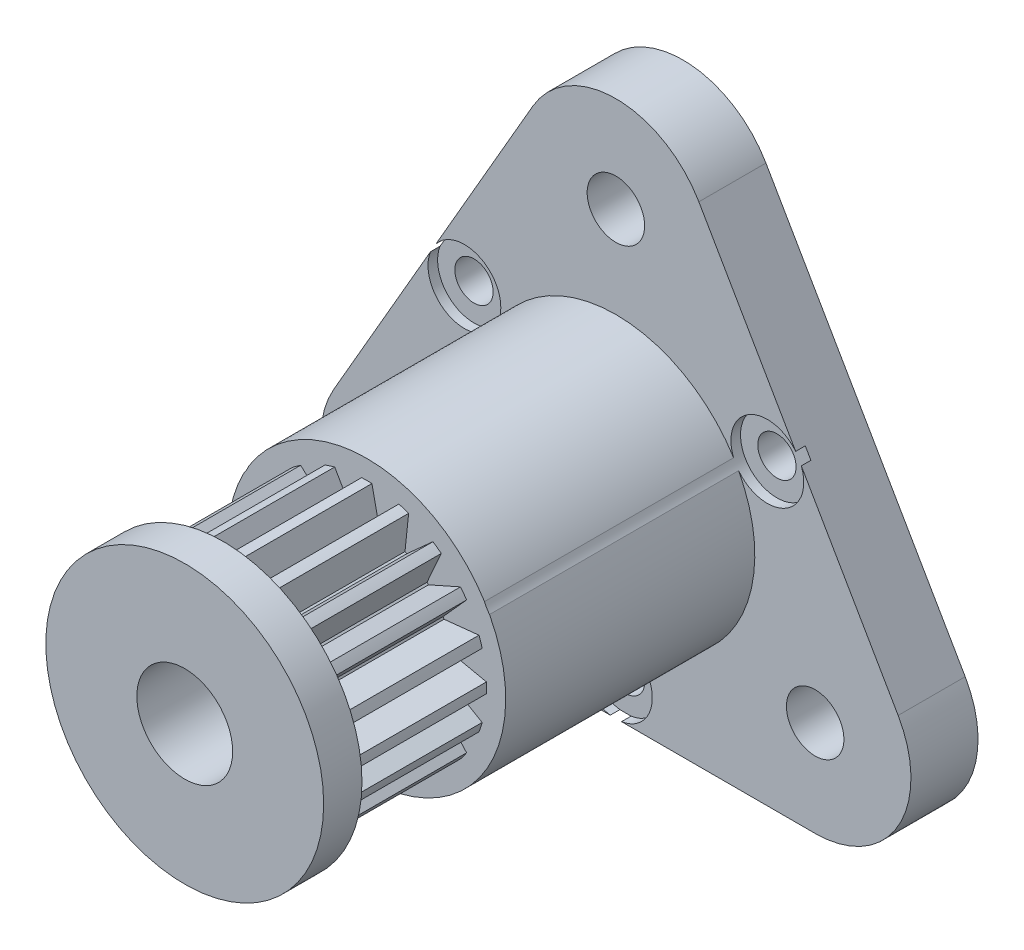
SolidWorks part; units mm, degrees
ref_plane "Front Plane" through (0, 0, 0) normal (0, 0, 1) x (1, 0, 0)
ref_plane "Top Plane" through (0, 0, 0) normal (0, 1, 0) x (1, 0, 0)
ref_plane "Right Plane" through (0, 0, 0) normal (1, 0, 0) x (0, 0, -1)
sketch "Sketch1" plane through (0, 0, 0) normal (0, 0, 1) x (1, 0, 0)
  line L0 (0, 12.0089) -> (0, 0) construction
  line L1 (0, 0) -> (-10.4, -6.0044) construction
  line L2 (0, 0) -> (10.4, -6.0044) construction
  line L3 (-14.7301, -3.5044) -> (-4.3301, 14.5089)
  line L4 (4.3301, 14.5089) -> (14.7301, -3.5044)
  line L5 (10.4, -11.0044) -> (-10.4, -11.0044)
  line L6 (7.5274, 4.346) -> (9.5301, 5.5022) construction
  line L7 (-5.1962, 3) -> (-7.5274, 4.346) construction
  line L8 (-7.5274, 4.346) -> (-9.5301, 5.5022) construction
  line L9 (0, -8.6919) -> (0, -11.0044) construction
  line L10 (0, 12.0089) -> (10.4, -6.0044) construction
  line L11 (10.4, -6.0044) -> (-10.4, -6.0044) construction
  line L12 (-10.4, -6.0044) -> (0, 12.0089) construction
  circle A0 centre (0, 12.0089) radius 1.5
  circle A1 centre (-10.4, -6.0044) radius 1.5
  circle A2 centre (10.4, -6.0044) radius 1.5
  arc A4 (4.3301, 14.5089) -> (-4.3301, 14.5089) centre (0, 12.0089) ccw
  arc A5 (-14.7301, -3.5044) -> (-10.4, -11.0044) centre (-10.4, -6.0044) ccw
  arc A6 (10.4, -11.0044) -> (14.7301, -3.5044) centre (10.4, -6.0044) ccw
  circle A7 centre (0, 0) radius 6 construction
  spline S0 degree 3 poles (12.0715, -6.9088) (-10.7674, -6.2165) (0.0526, 13.9086) (12.0715, -6.9088) (-10.7674, -6.2165) (0.0526, 13.9086) knots -1 -0.674106 -0.325894 0 0.325894 0.674106 1 1.325894 1.674106 2 only from (-5.2828, -3.05) to (-5.2828, -3.05) construction
  point P38 (0, 0)
  dimension "D4" = 3
  dimension "D5" = 12
  dimension "D6" = 10
  dimension "D1" = 20.8
  dimension "D2" = 120
  dimension "D3" = 120
  dimension "D9" = 3
extrude "Boss-Extrude1" add sketch "Sketch1" along normal blind 3.5
sketch "Sketch2" plane through (0, 0, 3.5) normal (0, 0, 1) x (1, 0, 0)
  line L0 (-10.4, -6.0044) -> (0, 0) construction
  line L1 (0, 0) -> (0, 12.0089) construction
  line L2 (0, 0) -> (10.4, -6.0044) construction
  circle A0 centre (0, 0) radius 7.25
  dimension "D2" = 14.5
extrude "Boss-Extrude2" add sketch "Sketch2" along normal blind 22.5
sketch "Sketch3" plane through (0, 0, 26) normal (0, 0, 1) x (1, 0, 0)
  circle A0 centre (0, 0) radius 2.5
  dimension "D1" = 5
extrude "Cut-Extrude1" cut sketch "Sketch3" against normal through all
ref_plane "Plane1" through (0, 0, 24) normal (0, 0, 1) x (1, 0, 0)
sketch "Sketch6" plane through (0, 0, 24) normal (0, 0, 1) x (1, 0, 0)
  line L0 (4.5, 0) -> (7.5, 0) construction
  line L1 (7.5, 0) -> (4.4528, 0.65)
  line L2 (7.5, 0) -> (4.4528, -0.65)
  line L3 (7.1329, -2.3176) -> (4.034, -1.9942)
  line L4 (7.1329, -2.3176) -> (4.4357, -0.7578)
  line L5 (6.0676, -4.4084) -> (3.2203, -3.1432)
  line L6 (6.0676, -4.4084) -> (3.9845, -2.0914)
  line L7 (4.4084, -6.0676) -> (2.0914, -3.9845)
  line L8 (4.4084, -6.0676) -> (3.1432, -3.2203)
  line L9 (2.3176, -7.1329) -> (0.7578, -4.4357)
  line L10 (2.3176, -7.1329) -> (1.9942, -4.034)
  line L11 (0, -7.5) -> (-0.65, -4.4528)
  line L12 (0, -7.5) -> (0.65, -4.4528)
  line L13 (-2.3176, -7.1329) -> (-1.9942, -4.034)
  line L14 (-2.3176, -7.1329) -> (-0.7578, -4.4357)
  line L15 (-4.4084, -6.0676) -> (-3.1432, -3.2203)
  line L16 (-4.4084, -6.0676) -> (-2.0914, -3.9845)
  line L17 (-6.0676, -4.4084) -> (-3.9845, -2.0914)
  line L18 (-6.0676, -4.4084) -> (-3.2203, -3.1432)
  line L19 (-7.1329, -2.3176) -> (-4.4357, -0.7578)
  line L20 (-7.1329, -2.3176) -> (-4.034, -1.9942)
  line L21 (-7.5, 0) -> (-4.4528, 0.65)
  line L22 (-7.5, 0) -> (-4.4528, -0.65)
  line L23 (-7.1329, 2.3176) -> (-4.034, 1.9942)
  line L24 (-7.1329, 2.3176) -> (-4.4357, 0.7578)
  line L25 (-6.0676, 4.4084) -> (-3.2203, 3.1432)
  line L26 (-6.0676, 4.4084) -> (-3.9845, 2.0914)
  line L27 (-4.4084, 6.0676) -> (-2.0914, 3.9845)
  line L28 (-4.4084, 6.0676) -> (-3.1432, 3.2203)
  line L29 (-2.3176, 7.1329) -> (-0.7578, 4.4357)
  line L30 (-2.3176, 7.1329) -> (-1.9942, 4.034)
  line L31 (0, 7.5) -> (0.65, 4.4528)
  line L32 (0, 7.5) -> (-0.65, 4.4528)
  line L33 (2.3176, 7.1329) -> (1.9942, 4.034)
  line L34 (2.3176, 7.1329) -> (0.7578, 4.4357)
  line L35 (4.4084, 6.0676) -> (3.1432, 3.2203)
  line L36 (4.4084, 6.0676) -> (2.0914, 3.9845)
  line L37 (6.0676, 4.4084) -> (3.9845, 2.0914)
  line L38 (6.0676, 4.4084) -> (3.2203, 3.1432)
  line L39 (7.1329, 2.3176) -> (4.4357, 0.7578)
  line L40 (7.1329, 2.3176) -> (4.034, 1.9942)
  line L41 (4.4357, 0.7578) -> (4.4528, 0.65)
  line L42 (4.4528, -0.65) -> (4.4357, -0.7578)
  line L43 (4.034, -1.9942) -> (3.9845, -2.0914)
  line L44 (3.2203, -3.1432) -> (3.1432, -3.2203)
  line L45 (2.0914, -3.9845) -> (1.9942, -4.034)
  line L46 (0.7578, -4.4357) -> (0.65, -4.4528)
  line L47 (-0.65, -4.4528) -> (-0.7578, -4.4357)
  line L48 (-1.9942, -4.034) -> (-2.0914, -3.9845)
  line L49 (-3.1432, -3.2203) -> (-3.2203, -3.1432)
  line L50 (-3.9845, -2.0914) -> (-4.034, -1.9942)
  line L51 (-4.4357, -0.7578) -> (-4.4528, -0.65)
  line L52 (-4.4528, 0.65) -> (-4.4357, 0.7578)
  line L53 (-4.034, 1.9942) -> (-3.9845, 2.0914)
  line L54 (-3.2203, 3.1432) -> (-3.1432, 3.2203)
  line L55 (-2.0914, 3.9845) -> (-1.9942, 4.034)
  line L56 (-0.7578, 4.4357) -> (-0.65, 4.4528)
  line L57 (0.65, 4.4528) -> (0.7578, 4.4357)
  line L58 (1.9942, 4.034) -> (2.0914, 3.9845)
  line L59 (3.1432, 3.2203) -> (3.2203, 3.1432)
  line L60 (3.9845, 2.0914) -> (4.034, 1.9942)
  circle A0 centre (0, 0) radius 4.5 construction
  circle A1 centre (0, 0) radius 7.5 construction
  circle A2 centre (0, 0) radius 9.5696
  point P67 (0, 0)
  point P106 (0, 0)
  dimension "D1" = 9
  dimension "D6" = 15
  dimension "D2" = 0.65
  dimension "D3" = 0.65
  dimension "D5" = 20
  dimension "D4" = 20
extrude "Cut-Extrude6" cut sketch "Sketch6" against normal blind 7.5
sketch "Sketch7" plane through (0, 0, 24) normal (0, 0, 1) x (1, 0, 0)
  circle A0 centre (0, 0) radius 6.25
  circle A1 centre (0, 0) radius 17.7758
  dimension "D1" = 12.5
extrude "Cut-Extrude7" cut sketch "Sketch7" against normal blind 7.5
sketch "Sketch8" plane through (0, 0, 3.5) normal (0, 0, 1) x (1, 0, 0)
  line L0 (9.5301, 5.5022) -> (6.2787, 3.625) construction
  line L2 (14.7301, -3.5044) -> (4.3301, 14.5089) construction
  line L3 (0, -11.0044) -> (0, -7.25) construction
  line L4 (-9.5301, 5.5022) -> (-6.2787, 3.625) construction
  circle A10 centre (0, 0) radius 7.25 construction
  circle A11 centre (7.9044, 4.5636) radius 1
  circle A12 centre (0, -9.1272) radius 1
  circle A13 centre (-7.9044, 4.5636) radius 1
  point P18 (0, 0)
  dimension "D1" = 2
extrude "Cut-Extrude8" cut sketch "Sketch8" against normal through all
sketch "Sketch9" plane through (0, 0, 3.5) normal (0, 0, 1) x (1, 0, 0)
  circle A9 centre (7.9044, 4.5636) radius 1.9
  circle A10 centre (0, -9.1272) radius 1.9
  circle A11 centre (-7.9044, 4.5636) radius 1.9
  point P8 (0, 0)
  dimension "D1" = 3.8
extrude "Cut-Extrude9" cut sketch "Sketch9" against normal blind 0.5 and the other way blind 13
